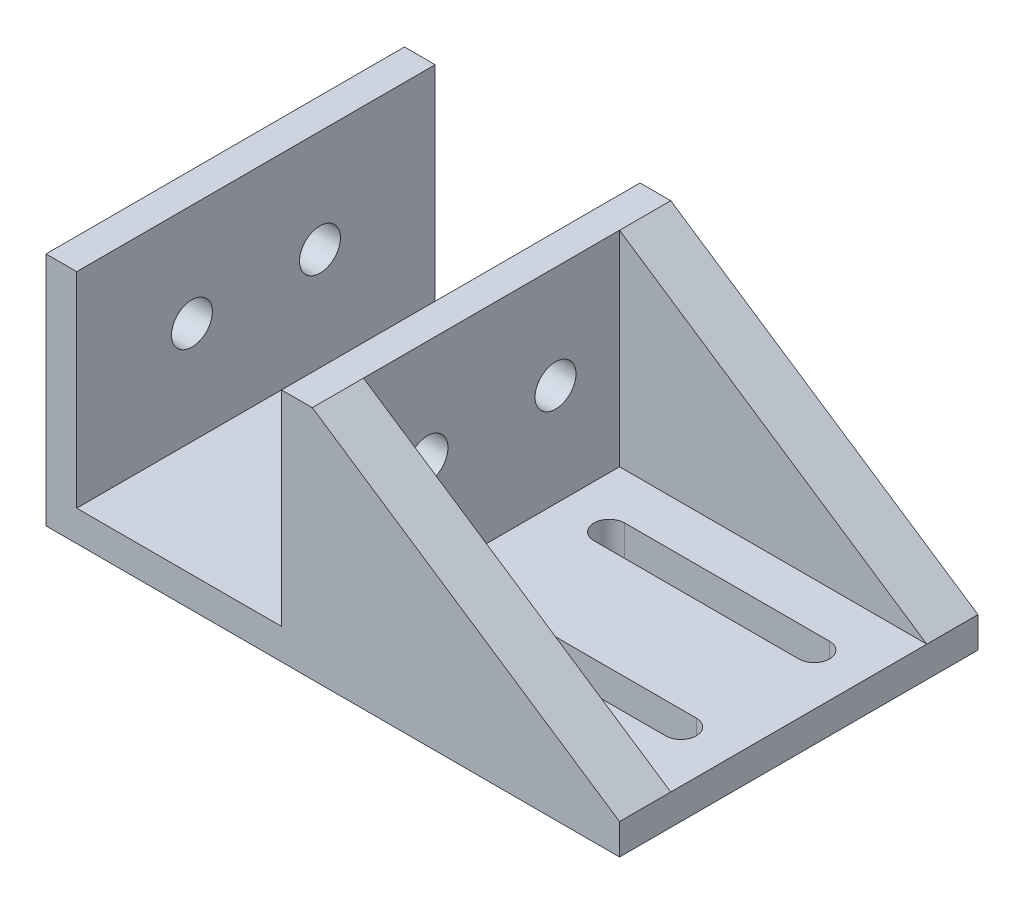
SolidWorks part; units mm, degrees
ref_plane "Front Plane" through (0, 0, 0) normal (0, 0, 1) x (1, 0, 0)
ref_plane "Top Plane" through (0, 0, 0) normal (0, 1, 0) x (1, 0, 0)
ref_plane "Right Plane" through (0, 0, 0) normal (1, 0, 0) x (0, 0, -1)
sketch "Sketch1" plane through (0, 0, 0) normal (0, 0, 1) x (1, 0, 0)
  line L13 (0, 23) -> (0, 0)
  line L14 (0, 0) -> (56, 0)
  line L15 (56, 0) -> (56, 3)
  line L16 (56, 3) -> (26, 3)
  line L17 (26, 3) -> (26, 23)
  line L18 (26, 23) -> (23, 23)
  line L19 (23, 23) -> (23, 3)
  line L20 (23, 3) -> (3, 3)
  line L21 (3, 3) -> (3, 23)
  line L22 (3, 23) -> (0, 23)
  point P0 (14.6674, 12.42)
  dimension "D1" = 20
  dimension "D2" = 3
  dimension "D3" = 30
extrude "Boss-Extrude1" add sketch "Sketch1" along normal blind 35
sketch "Sketch3" plane through (0, 3, 0) normal (0, 1, 0) x (1, 0, 0)
  line L0 (31, -11) -> (51, -11) construction
  line L1 (31, -9.5) -> (51, -9.5)
  line L2 (31, -12.5) -> (51, -12.5)
  line L3 (26, -17.5) -> (56, -17.5) construction
  line L4 (26, -35) -> (26, 0) construction
  line L5 (56, -35) -> (56, 0) construction
  line L6 (41, 0) -> (41, -11) construction
  line L7 (56, 0) -> (26, 0) construction
  line L8 (41, -11) -> (41, -17.5) construction
  line L9 (31, -24) -> (51, -24) construction
  line L10 (31, -25.5) -> (51, -25.5)
  line L11 (31, -22.5) -> (51, -22.5)
  arc A0 (31, -9.5) -> (31, -12.5) centre (31, -11) ccw
  arc A1 (51, -12.5) -> (51, -9.5) centre (51, -11) ccw
  arc A2 (31, -25.5) -> (31, -22.5) centre (31, -24) cw
  arc A3 (51, -22.5) -> (51, -25.5) centre (51, -24) cw
  point P2 (41, -11)
  point P20 (41, -24)
  dimension "D1" = 20
  dimension "D2" = 3
  dimension "D3" = 10
extrude "Cut-Extrude2" cut sketch "Sketch3" against normal through all both
sketch "Sketch4" plane through (0, 0, 35) normal (0, 0, 1) x (1, 0, 0)
  line L0 (26, 23) -> (26, 3)
  line L1 (26, 3) -> (56, 3)
  line L2 (56, 3) -> (26, 23)
extrude "Boss-Extrude2" add sketch "Sketch4" against normal through all
sketch "Sketch5" plane through (0, 23, 0) normal (0, 1, 0) x (1, 0, 0)
  line L0 (26, -17.5) -> (56, -17.5) construction
  line L1 (26, -35) -> (26, 0) construction
  line L2 (56, -35) -> (56, 0) construction
  line L3 (56, -35) -> (26, -35) construction
  line L4 (26, -5) -> (56, -5)
  line L5 (26, -5) -> (26, -30)
  line L6 (26, -30) -> (56, -30)
  line L7 (56, -5) -> (56, -30)
  line L8 (26, -5) -> (56, -30) construction
  line L9 (26, -30) -> (56, -5) construction
  point P6 (41, -17.5)
  dimension "D1" = 5
extrude "Cut-Extrude3" cut sketch "Sketch5" against normal up to surface (20 mm away) up to face at (13, 3, 17.5)
sketch "Sketch6" plane through (26, 0, 0) normal (1, 0, 0) x (0, 0, -1)
  line L0 (-30, 13) -> (-23.75, 13) construction
  line L1 (-30, 23) -> (-30, 3) construction
  line L2 (-23.75, 13) -> (-17.5, 13) construction
  line L3 (-17.5, 13) -> (-17.5, 23) construction
  line L4 (-5, 23) -> (-30, 23) construction
  circle A0 centre (-23.75, 13) radius 2
  circle A1 centre (-11.25, 13) radius 2
  dimension "D1" = 4
extrude "Cut-Extrude4" cut sketch "Sketch6" against normal through all
